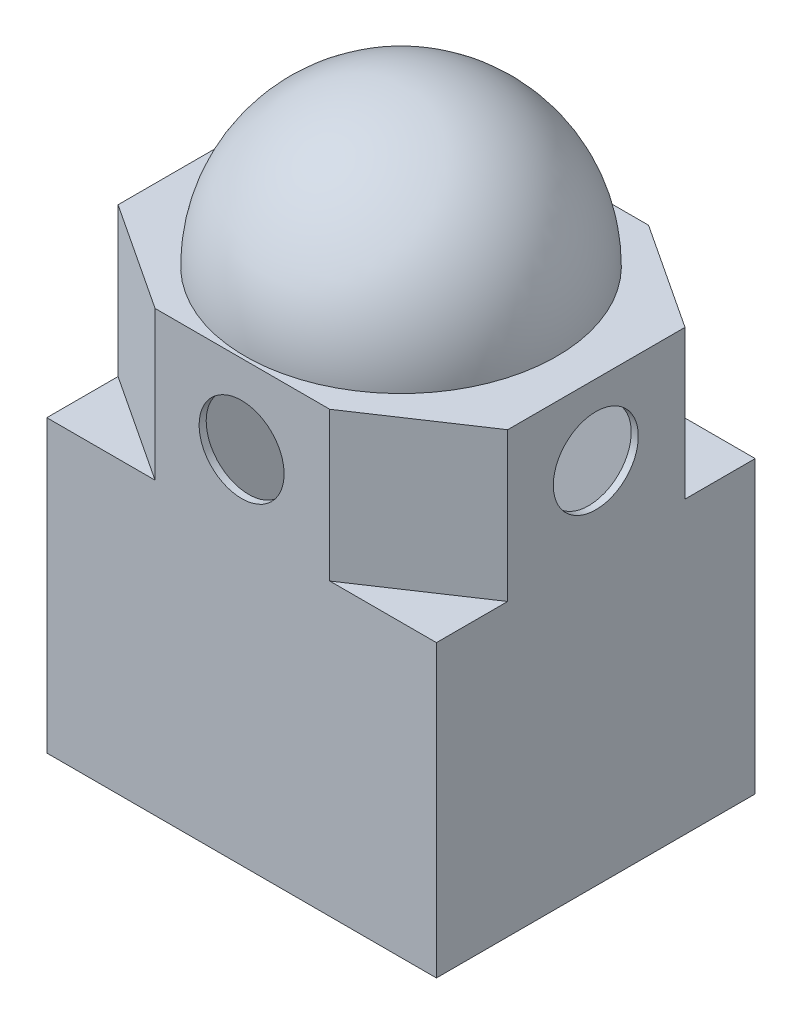
SolidWorks part; units mm, degrees
other "Markup1"
sketch "Sketch16" plane through (-55, 0, 45) normal (-0.0358, -0.9991, 0.0226) x (0.0076, 0.0224, 0.9997)
ref_plane "Front Plane" through (0, 0, 0) normal (0, 0, 1) x (1, 0, 0)
ref_plane "Top Plane" through (0, 0, 0) normal (0, 1, 0) x (1, 0, 0)
ref_plane "Right Plane" through (0, 0, 0) normal (1, 0, 0) x (0, 0, -1)
sketch "Sketch1" plane through (0, 0, 0) normal (0, 1, 0) x (1, 0, 0)
  line L0 (-53, 43) -> (53, 43)
  line L1 (-55, 45) -> (55, 45)
  line L2 (-55, 45) -> (-55, -45)
  line L3 (-55, -45) -> (55, -45)
  line L4 (55, 45) -> (55, -45)
  line L5 (-55, 45) -> (55, -45) construction
  line L6 (-55, -45) -> (55, 45) construction
  line L7 (53, 43) -> (53, -43)
  line L8 (-53, -43) -> (53, -43)
  line L9 (-53, 43) -> (-53, -43)
  point P0 (0, 0)
  dimension "D1" = 110
  dimension "D2" = 90
  dimension "D4" = 110
  dimension "D3" = 2
extrude "Boss-Extrude1" add sketch "Sketch1" along normal blind 80
sketch "Sketch2" plane through (0, 80, 0) normal (0, 1, 0) x (1, 0, 0)
  line L1 (-55, 45) -> (55, 45)
  line L2 (-55, 45) -> (-55, -45)
  line L3 (-55, -45) -> (55, -45)
  line L4 (55, 45) -> (55, -45)
  line L5 (-55, 45) -> (55, -45) construction
  line L6 (-55, -45) -> (55, 45) construction
  point P0 (0, 0)
extrude "Boss-Extrude2" add sketch "Sketch2" along normal blind 2
sketch "Sketch3" plane through (0, 82, 0) normal (0, 1, 0) x (1, 0, 0)
  line L0 (55, 25.178) -> (24.8835, 45)
  line L1 (55, -45) -> (55, 45) construction
  line L2 (55, 45) -> (-55, 45) construction
  line L3 (24.8835, 45) -> (-25.0307, 45)
  line L4 (-25.0307, 45) -> (-55, 25.178)
  line L5 (-55, 45) -> (-55, -45) construction
  line L6 (-55, 25.178) -> (-55, -24.8835)
  line L7 (-55, -24.8835) -> (-24.4361, -45)
  line L8 (-55, -45) -> (55, -45) construction
  line L9 (-24.4361, -45) -> (24.8835, -45)
  line L10 (24.8835, -45) -> (55, -24.8835)
  line L11 (55, -24.8835) -> (55, 25.178)
  line L12 (53, 24.1) -> (24.2844, 43)
  line L13 (24.2844, 43) -> (-24.4292, 43)
  line L14 (-24.4292, 43) -> (-53, 24.1029)
  line L15 (-53, 24.1029) -> (-53, -23.8055)
  line L16 (-53, -23.8055) -> (-23.837, -43)
  line L17 (-23.837, -43) -> (24.277, -43)
  line L18 (24.277, -43) -> (53, -23.8143)
  line L19 (53, -23.8143) -> (53, 24.1)
  dimension "D1" = 2
extrude "Boss-Extrude3" add sketch "Sketch3" along normal blind 40
sketch "Sketch7" plane through (0, 82, 0) normal (0, 1, 0) x (1, 0, 0)
  line L0 (-24.4292, 43) -> (-53, 24.1029)
  line L1 (-53, 24.1029) -> (-53, -23.8055)
  line L2 (-53, 24.1029) -> (-53, -23.8055) construction
  line L3 (-53, 24.1029) -> (-53, -23.8055) construction
  line L4 (-53, -23.8055) -> (-23.837, -43)
  line L5 (-23.837, -43) -> (24.277, -43)
  line L6 (24.277, -43) -> (53, -23.8143)
  line L7 (53, -23.8143) -> (53, 24.1)
  line L8 (53, 24.1) -> (24.2844, 43) construction
  line L9 (53, -23.8143) -> (53, 24.1) construction
  line L10 (53, 24.1) -> (24.2844, 43)
  line L11 (24.2844, 43) -> (-24.4292, 43)
extrude "Cut-Extrude1" cut sketch "Sketch7" against normal blind 40
sketch "Sketch8" plane through (0, 122, 0) normal (0, 1, 0) x (1, 0, 0)
  line L1 (24.8835, 45) -> (55, 25.178)
  line L2 (55, 25.178) -> (55, -24.8835)
  line L3 (55, -24.8835) -> (55, 25.178) construction
  line L4 (55, -24.8835) -> (24.8835, -45)
  line L5 (24.8835, -45) -> (55, -24.8835) construction
  line L6 (24.8835, -45) -> (-24.4361, -45)
  line L7 (-24.4361, -45) -> (24.8835, -45) construction
  line L8 (-24.4361, -45) -> (-55, -24.8835)
  line L9 (-55, -24.8835) -> (-55, 25.178)
  line L10 (-55, 25.178) -> (-25.0307, 45)
  line L11 (-25.0307, 45) -> (24.8835, 45)
extrude "Boss-Extrude4" add sketch "Sketch8" along normal blind 2
sketch "Sketch9" plane through (0, 124, 0) normal (0, 1, 0) x (1, 0, 0)
  circle A0 centre (0, 0) radius 44.4822
sketch "Sketch11" plane through (0, 124, 0) normal (0, 1, 0) x (1, 0, 0)
  line L1 (11.5, 6.5) -> (-11.5, 6.5)
  line L2 (11.5, 6.5) -> (11.5, -6.5)
  line L3 (11.5, -6.5) -> (-11.5, -6.5)
  line L4 (-11.5, 6.5) -> (-11.5, -6.5)
  line L5 (11.5, 6.5) -> (-11.5, -6.5) construction
  line L6 (11.5, -6.5) -> (-11.5, 6.5) construction
  point P0 (0, 0)
  dimension "D1" = 23
  dimension "D2" = 13
extrude "Cut-Extrude2" cut sketch "Sketch11" against normal blind 13
sketch "Sketch12" plane through (0, 124, 0) normal (0, 1, 0) x (1, 0, 0)
  line L0 (43.9958, 0) -> (-43.9958, 0) construction
  line L1 (43.9958, 0) -> (-43.9958, 0) construction
  line L3 (41.9482, -2) -> (-41.9482, -2) construction
  line L4 (41.9482, -2) -> (41.9482, 0)
  line L5 (-41.9482, -2) -> (-41.9482, 0)
  arc A0 (-43.9958, 0) -> (43.9958, 0) centre (0, 0) ccw
  arc A1 (-41.9482, -2) -> (41.9482, -2) centre (0, 0) ccw
  dimension "D1" = 2
revolve "Revolve-Thin3" add sketch "Sketch12" angle 180 about L0 wall 2
sketch "Sketch13" plane through (0, 0, -45) normal (0, 0, -1) x (-1, 0, 0)
  circle A0 centre (0, 101.7217) radius 12
  dimension "D1" = 24
extrude "Cut-Extrude3" cut sketch "Sketch13" against normal blind 97
sketch "Sketch14" plane through (-55, 0, 0) normal (-1, 0, 0) x (0, 0, 1)
  circle A0 centre (0, 103.9806) radius 12
  dimension "D1" = 24
extrude "Cut-Extrude4" cut sketch "Sketch14" against normal blind 112
